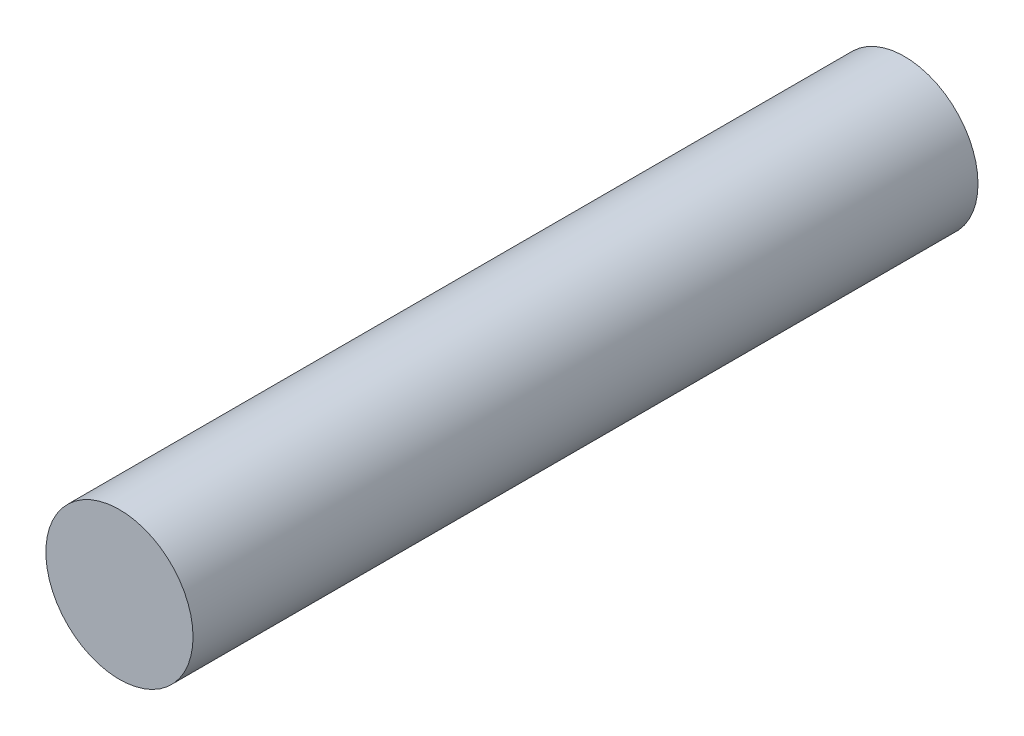
SolidWorks part; units mm, degrees
ref_plane "Front Plane" through (0, 0, 0) normal (0, 0, 1) x (1, 0, 0)
ref_plane "Top Plane" through (0, 0, 0) normal (0, 1, 0) x (1, 0, 0)
ref_plane "Right Plane" through (0, 0, 0) normal (1, 0, 0) x (0, 0, -1)
sketch "Sketch1" plane through (0, 0, 0) normal (0, 0, 1) x (1, 0, 0)
  circle A0 centre (0, 0) radius 2.3813
  dimension "D1" = 4.7625
extrude "Boss-Extrude1" add sketch "Sketch1" against normal blind 25.4
